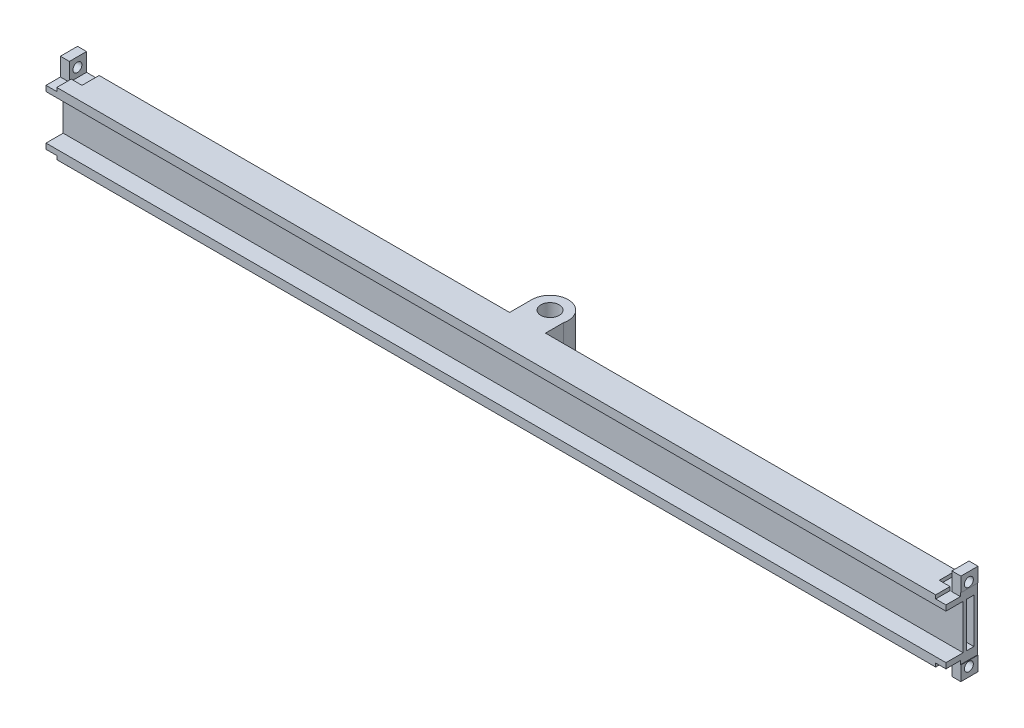
SolidWorks part; units mm, degrees
material "PLA"
ref_plane "Front Plane" through (0, 0, 0) normal (1, 0, 0) x (0, 1, 0)
ref_plane "Top Plane" through (0, 0, 0) normal (0, 0, 1) x (0, 1, 0)
ref_plane "Right Plane" through (0, 0, 0) normal (0, 1, 0) x (-1, 0, 0)
sketch "Sketch1" plane through (0, 0, 0) normal (1, 0, 0) x (0, 1, 0)
  line L16 (0, 4.7625) -> (-2.5, 4.7625)
  line L17 (0, 0) -> (12.3825, 0)
  line L18 (0, 0) -> (0, 4.7625)
  line L19 (0, 4.7625) -> (12.3825, 4.7625) construction
  line L20 (12.3825, 0) -> (12.3825, 4.7625)
  line L21 (-2.5, 4.7625) -> (-2.5, -4)
  line L22 (-2.5, -4) -> (14.8825, -4)
  line L23 (14.8825, -4) -> (14.8825, 4.7625)
  line L24 (12.3825, 4.7625) -> (14.8825, 4.7625)
  dimension "D1" = 4.7625
  dimension "D2" = 12.3825
  dimension "D3" = 2.5
  dimension "D4" = 4
extrude "Boss-Extrude1" add sketch "Sketch1" along normal blind 250
sketch "Sketch3" plane through (0, -2.5, 0) normal (0, -1, 0) x (1, 0, 0)
  line L0 (120.0194, -4) -> (129.9806, -4)
  line L1 (250, -4) -> (0, -4) construction
  line L2 (129.9806, -4) -> (129.9806, -9)
  line L3 (120.0194, -4) -> (120.0194, -10.1759)
  line L4 (0, 4.7625) -> (0, -4) construction
  arc A0 (120.0194, -10.1759) -> (129.9806, -9) centre (125.0694, -10.1759) ccw
  circle A1 centre (125.0694, -10.1759) radius 2.55
  point P5 (125, -4)
  dimension "D2" = 5.1
  dimension "D3" = 5
  dimension "D4" = 125
extrude "Boss-Extrude2" add sketch "Sketch3" against normal up to surface (17.3825 mm away) up to face at (125, 14.8825, 0.3813)
sketch "Sketch6" plane through (0, -2.5, 0) normal (0, -1, 0) x (1, 0, 0)
  line L0 (120.0194, -4) -> (0, -4) construction
  line L1 (117.5385, -4) -> (131.3691, -4)
  line L2 (117.5385, -4) -> (117.5385, -13.6365)
  line L3 (117.5385, -13.6365) -> (131.3691, -13.6365)
  line L4 (131.3691, -4) -> (131.3691, -13.6365)
extrude "Cut-Extrude2" [suppressed] cut sketch "Sketch6" against normal blind 5
sketch "Sketch7" plane through (0, 14.8825, 0) normal (0, 1, 0) x (-1, 0, 0)
  line L0 (-250, -4) -> (-129.9806, -4) construction
  line L1 (-136.5723, -4) -> (-116.3235, -4)
  line L2 (-136.5723, -4) -> (-136.5723, -14.7915)
  line L3 (-136.5723, -14.7915) -> (-116.3235, -14.7915)
  line L4 (-116.3235, -4) -> (-116.3235, -14.7915)
extrude "Cut-Extrude3" [suppressed] cut sketch "Sketch7" against normal blind 5
sketch "Sketch8" plane through (250, 0, 0) normal (1, 0, 0) x (0, 1, 0)
  line L0 (6.1913, 0) -> (6.1913, -4) construction
  line L5 (12.3825, 0) -> (0, 0) construction
  line L6 (14.8825, -4) -> (-2.5, -4) construction
  line L11 (0, -3) -> (12.3825, -3)
  line L12 (0, -3) -> (0, -1)
  line L13 (0, -1) -> (12.3825, -1)
  line L14 (12.3825, -3) -> (12.3825, -1)
  line L15 (0, -3) -> (12.3825, -1) construction
  line L16 (0, -1) -> (12.3825, -3) construction
  point P6 (6.1913, -2)
  dimension "D1" = 12.3825
extrude "Cut-Extrude4" cut sketch "Sketch8" against normal through all
sketch "Sketch9" plane through (0, 0, -4) normal (0, 0, -1) x (-1, 0, 0)
  line L0 (-117.5194, -2.5) -> (-117.5194, 14.8825) construction
  line L1 (-120.0194, -2.5) -> (0, -2.5) construction
  line L2 (-120.0194, 14.8825) -> (0, 14.8825) construction
  line L3 (-120.0194, 14.8825) -> (-120.0194, -2.5) construction
  line L4 (-116.5194, 12.3825) -> (-118.5194, 12.3825)
  line L5 (-116.5194, 12.3825) -> (-116.5194, 0)
  line L6 (-116.5194, 0) -> (-118.5194, 0)
  line L7 (-118.5194, 12.3825) -> (-118.5194, 0)
  line L8 (-116.5194, 12.3825) -> (-118.5194, 0) construction
  line L9 (-116.5194, 0) -> (-118.5194, 12.3825) construction
  point P6 (-117.5194, 6.1913)
  dimension "D3" = 2.5
  dimension "D1" = 12.3825
extrude "Cut-Extrude5" cut sketch "Sketch9" against normal up to next (1 mm away)
ref_plane "Plane1" through (125.0694, 0, 0) normal (-1, 0, 0) x (0, 0, 1)
mirror "Mirror1" about plane through (125.0694, 0, 0) normal (-1, 0, 0) of "Cut-Extrude5"
sketch "Sketch10" plane through (0, 0, 4.7625) normal (0, 0, 1) x (1, 0, 0)
  line L1 (0, 14.8825) -> (2.5, 14.8825)
  line L2 (0, 14.8825) -> (0, 18.8912)
  line L3 (0, 18.8912) -> (2.5, 18.8912)
  line L4 (2.5, 14.8825) -> (2.5, 18.8912)
  line L5 (0, -2.5) -> (2.5, -2.5)
  line L6 (0, -2.5) -> (0, -6.5088)
  line L7 (0, -6.5088) -> (2.5, -6.5088)
  line L8 (2.5, -2.5) -> (2.5, -6.5088)
  dimension "D2" = 25.4
extrude "Boss-Extrude3" add sketch "Sketch10" against normal up to surface (8.7625 mm away) up to face at (117.5194, 6.1913, -4)
mirror "Mirror2" about plane through (125.0694, 0, 0) normal (-1, 0, 0) of "Boss-Extrude3"
sketch "Sketch11" plane through (250.1388, 0, 0) normal (1, 0, 0) x (0, 1, 0)
  circle A0 centre (16.3513, -1.46) radius 1.25 construction
  circle A1 centre (-3.9687, -1.46) radius 1.25 construction
  circle A2 centre (16.3513, -1.46) radius 1.25
  circle A3 centre (-3.9687, -1.46) radius 1.25
extrude "Cut-Extrude6" cut sketch "Sketch11" against normal up to surface (247.6388 mm away)
mirror "Mirror3" about plane through (125.0694, 0, 0) normal (-1, 0, 0) of "Cut-Extrude6"
sketch "Sketch14" plane through (0, 0, 4.7625) normal (0, 0, 1) x (1, 0, 0)
  line L0 (0, 6.1912) -> (17.1619, 6.1912) construction
  line L1 (0, -6.5088) -> (3, -6.5088)
  line L2 (0, -6.5088) -> (0, -1.5088)
  line L3 (0, -1.5088) -> (3, -1.5088)
  line L4 (3, -6.5088) -> (3, -1.5088)
  line L5 (0, 12.3825) -> (0, 0) construction
  line L6 (0, 13.8912) -> (3, 13.8912)
  line L7 (3, 18.8912) -> (3, 13.8912)
  line L8 (0, 18.8912) -> (3, 18.8912)
  line L9 (0, 18.8912) -> (0, 13.8912)
  dimension "D1" = 5
  dimension "D2" = 3
extrude "Cut-Extrude7" cut sketch "Sketch14" against normal blind 4
mirror "Mirror4" about plane through (125.0694, 0, 0) normal (-1, 0, 0) of "Cut-Extrude7"
sketch "Sketch15" plane through (0, -2.5, 0) normal (0, -1, 0) x (-1, 0, 0)
  line L0 (-3, -0.7625) -> (-2.5, -0.7625) construction
  line L1 (-2.5, 4) -> (-6, 4)
  line L2 (-2.5, 4) -> (-2.5, -0.7625)
  line L3 (-2.5, -0.7625) -> (-6, -0.7625)
  line L4 (-6, 4) -> (-6, -0.7625)
  line L5 (0, 4) -> (0, -0.7625) construction
  dimension "D1" = 6
extrude "Cut-Extrude9" cut sketch "Sketch15" against normal blind 1 contours L4 L3 L2 L1
ref_plane "Plane3" through (0, 6.1913, 0) normal (0, 1, 0) x (1, 0, 0)
mirror "Mirror7" about plane through (0, 6.1913, 0) normal (0, 1, 0) of "Cut-Extrude9"
mirror "Mirror8" about plane through (125.0694, 0, 0) normal (-1, 0, 0) of "Mirror7", "Cut-Extrude9"
equation "\"D1@Sketch1\"=\"ball_diameter\" * 0.25"
equation "\"D2@Sketch1\"=\"ball_diameter\" * 0.65"
equation "\"D3@Sketch1\"=\"wall_thickness\""
equation "\"D4@Sketch1\"=0.4cm"
equation "\"D1@Boss-Extrude1\"=\"track_length\""
equation "\"D2@Sketch3\"=\"axle\" + 0.01"
equation "\"ball_diameter\"= 0.75in"
equation "\"wall_thickness\" = 0.25cm"
equation "\"track_length\" = 25cm"
equation "\"axle\" = 5mm"
equation "\"D3@Sketch3\"=\"axle\" * 1"
equation "\"D4@Sketch3\"=\"track_length\" / 2"
equation "\"pillar_width\" = 2.75cm"
equation "\"D1@Sketch9\"=\"ball_diameter\" * 0.65"
equation "\"D1@Sketch8\"=\"ball_diameter\"*0.65"
equation "\"D1@Sketch10\"=\"wall_thickness\""
equation "\"D2@Sketch14\"=0.3"
